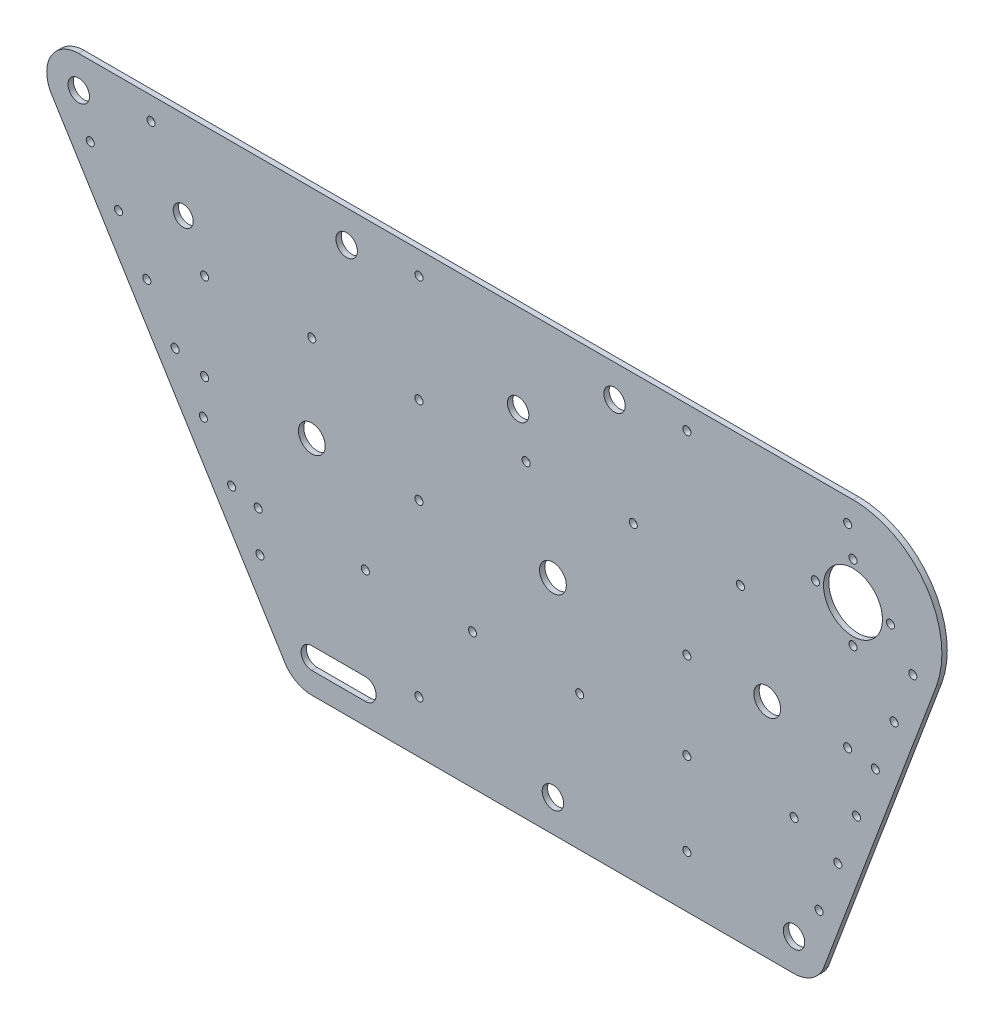
SolidWorks part; units mm, degrees
ref_plane "Front Plane" through (0, 0, 0) normal (0, 0, 1) x (1, 0, 0)
ref_plane "Top Plane" through (0, 0, 0) normal (0, 1, 0) x (1, 0, 0)
ref_plane "Right Plane" through (0, 0, 0) normal (1, 0, 0) x (0, 0, -1)
sketch "Sketch2" plane through (0, 0, 0) normal (0, 0, 1) x (1, 0, 0)
  line L0 (-106.0052, 144.9436) -> (182.9631, 145.1977)
  line L1 (160.992, -19) -> (-18.999, -19)
  line L2 (171.9001, -12) -> (214.069, 100.3323)
  line L3 (-18.999, -3) -> (1, -3)
  line L4 (0.9999, -11) -> (-18.9991, -11)
  line L5 (-29.7001, -12.4286) -> (-116.0855, 126.6112)
  line L6 (-18.9991, -18) -> (-18.8768, -17.9993)
  ellipse E0 centre (-105.9947, 133) end of major axis (-105.9947, 137) minor radius 3.9998
  ellipse E1 centre (160.992, -7) end of major axis (160.992, -3) minor radius 3.9998
  ellipse E2 centre (-18.9991, -7) end of major axis (-18.9991, -11) minor radius 3.9998 (-18.999, -3) -> (-18.9991, -11) ccw
  ellipse E3 centre (182.9908, 112) end of major axis (182.9908, 123) minor radius 10.9995
  ellipse E4 centre (-105.9947, 133) end of major axis (-105.9947, 144.9436) minor radius 11.943 (-106.0052, 144.9436) -> (-116.0855, 126.6112) ccw
  ellipse E5 centre (182.9908, 112) end of major axis (182.9909, 145.1977) minor radius 33.196 (214.069, 100.3323) -> (182.9617, 145.1977) ccw
  ellipse E6 centre (1, -7) end of major axis (1, -3) minor radius 3.9998 (0.9999, -11) -> (1, -3) ccw
  ellipse E7 centre (182.9908, 126) end of major axis (182.9908, 127.5) minor radius 1.4999
  ellipse E8 centre (196.9901, 112) end of major axis (196.9901, 113.5) minor radius 1.4999
  ellipse E9 centre (168.9915, 112) end of major axis (168.9915, 113.5) minor radius 1.4999
  ellipse E10 centre (182.9908, 98) end of major axis (182.9908, 99.5) minor radius 1.4999
  ellipse E11 centre (-18.9991, -7) end of major axis (-18.999, 5) minor radius 11.9994 (-29.7019, -12.4256) -> (-18.999, -19) ccw
  ellipse E12 centre (160.992, -7) end of major axis (160.992, 5) minor radius 11.9994 (160.992, -19) -> (171.9001, -12) ccw
  ellipse E13 centre (120.9939, 0.5) end of major axis (120.994, 2) minor radius 1.4999
  ellipse E14 centre (20.9989, 0.5) end of major axis (20.9989, 2) minor radius 1.4999
  ellipse E15 centre (120.9939, 64) end of major axis (120.994, 65.5) minor radius 1.4999
  ellipse E16 centre (20.9989, 64) end of major axis (20.9989, 65.5) minor radius 1.4999
  ellipse E17 centre (-58.997, 64) end of major axis (-58.997, 65.5) minor radius 1.4999
  ellipse E18 centre (180.9909, 64) end of major axis (180.9909, 65.5) minor radius 1.4999
  ellipse E19 centre (-78.996, 136.5) end of major axis (-78.996, 138) minor radius 1.4999
  ellipse E20 centre (20.9989, 136.5) end of major axis (20.9989, 138) minor radius 1.4999
  ellipse E21 centre (120.9939, 136.5) end of major axis (120.994, 138) minor radius 1.4999
  ellipse E22 centre (60.9969, 96.5) end of major axis (60.9969, 98) minor radius 1.4999
  ellipse E23 centre (140.9929, 96.5) end of major axis (140.9929, 98) minor radius 1.4999
  ellipse E24 centre (160.992, 31.5) end of major axis (160.992, 33) minor radius 1.4999
  ellipse E25 centre (80.996, 31.5) end of major axis (80.996, 33) minor radius 1.4999
  ellipse E26 centre (-18.9991, 96.5) end of major axis (-18.9991, 98) minor radius 1.4999
  ellipse E27 centre (-38.998, 31.5) end of major axis (-38.998, 33) minor radius 1.4999
  ellipse E28 centre (-18.9991, 64) end of major axis (-18.999, 69) minor radius 4.9997
  ellipse E29 centre (70.9964, 64) end of major axis (70.9965, 69) minor radius 4.9997
  ellipse E30 centre (150.9924, 64) end of major axis (150.9924, 69) minor radius 4.9997
  ellipse E31 centre (-101.6892, 118.5984) end of major axis (-101.6892, 120.0984) minor radius 1.4999
  ellipse E32 centre (-91.1347, 101.6106) end of major axis (-91.1347, 103.1106) minor radius 1.4999
  ellipse E33 centre (-80.5803, 84.623) end of major axis (-80.5803, 86.123) minor radius 1.4999
  ellipse E34 centre (-70.0255, 67.6347) end of major axis (-70.0255, 69.1347) minor radius 1.4999
  ellipse E35 centre (-59.4708, 50.6466) end of major axis (-59.4708, 52.1466) minor radius 1.4999
  ellipse E36 centre (-48.9163, 33.6588) end of major axis (-48.9163, 35.1588) minor radius 1.4999
  ellipse E37 centre (-38.3619, 16.6713) end of major axis (-38.3619, 18.1713) minor radius 1.4999
  ellipse E38 centre (205.3225, 99.7958) end of major axis (205.3225, 101.2958) minor radius 1.4999
  ellipse E39 centre (198.3244, 81.0602) end of major axis (198.3244, 82.5602) minor radius 1.4999
  ellipse E40 centre (191.3265, 62.3248) end of major axis (191.3265, 63.8248) minor radius 1.4999
  ellipse E41 centre (184.3286, 43.5896) end of major axis (184.3286, 45.0896) minor radius 1.4999
  ellipse E42 centre (177.3307, 24.8545) end of major axis (177.3307, 26.3545) minor radius 1.4999
  ellipse E43 centre (170.3325, 6.1186) end of major axis (170.3325, 7.6186) minor radius 1.4999
  ellipse E44 centre (180.9909, 136.5) end of major axis (180.9909, 138) minor radius 1.4999
  ellipse E45 centre (20.9989, 96.5) end of major axis (20.9989, 98) minor radius 1.4999
  ellipse E46 centre (100.995, 96.5) end of major axis (100.995, 98) minor radius 1.4999
  ellipse E47 centre (-58.9971, 96.5) end of major axis (-58.997, 98) minor radius 1.4999
  ellipse E48 centre (0.9999, 31.5) end of major axis (1, 33) minor radius 1.4999
  ellipse E49 centre (40.9979, 31.5) end of major axis (40.9979, 33) minor radius 1.4999
  ellipse E50 centre (120.9939, 31.5) end of major axis (120.994, 33) minor radius 1.4999
  ellipse E51 centre (-66.9967, 112) end of major axis (-66.9966, 115.75) minor radius 3.7498
  ellipse E52 centre (57.9971, 112) end of major axis (57.9971, 116) minor radius 3.9998
  ellipse E53 centre (-5.9997, 133) end of major axis (-5.9997, 137) minor radius 3.9998
  ellipse E54 centre (93.9952, 133) end of major axis (93.9952, 137) minor radius 3.9998
  ellipse E55 centre (70.9964, -7) end of major axis (70.9965, -3) minor radius 3.9998
  point P1 (120.9939, 136.5)
  point P2 (-78.996, 136.5)
  point P345 (120.9939, 0.5)
  point P346 (20.9989, 0.5)
  point P347 (-38.998, 31.5)
  point P348 (-38.3619, 16.6713)
  point P349 (-48.9163, 33.6588)
  point P350 (-59.4708, 50.6466)
  point P351 (-58.997, 64)
  point P352 (-70.0255, 67.6347)
  point P353 (-80.5803, 84.623)
  point P354 (-91.1347, 101.6106)
  point P355 (-101.6892, 118.5984)
  point P356 (-58.9971, 96.5)
extrude "Boss-Extrude1" add sketch "Sketch2" along normal blind 2
